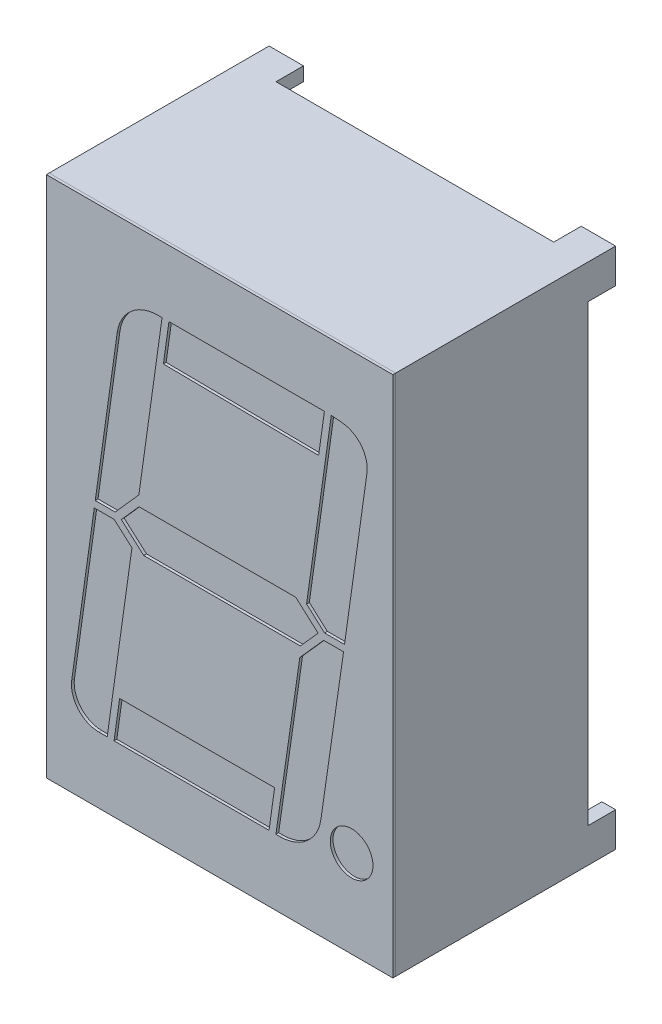
SolidWorks part; units mm, degrees
ref_plane "Front Plane" through (0, 0, 0) normal (0, 0, 1) x (1, 0, 0)
ref_plane "Top Plane" through (0, 0, 0) normal (0, 1, 0) x (1, 0, 0)
ref_plane "Right Plane" through (0, 0, 0) normal (1, 0, 0) x (0, 0, -1)
sketch "Sketch1" plane through (0, 0, 0) normal (0, 0, 1) x (1, 0, 0)
  line L1 (-6.3, -9.5) -> (6.3, -9.5)
  line L2 (-6.3, -9.5) -> (-6.3, 9.5)
  line L3 (-6.3, 9.5) -> (6.3, 9.5)
  line L4 (6.3, -9.5) -> (6.3, 9.5)
  line L5 (-6.3, -9.5) -> (6.3, 9.5) construction
  line L6 (-6.3, 9.5) -> (6.3, -9.5) construction
  point P0 (0, 0)
  dimension "D1" = 12.6
  dimension "D2" = 19
extrude "Boss-Extrude1" add sketch "Sketch1" along normal blind 7
sketch "Sketch2" plane through (0, 0, 0) normal (0, 0, -1) x (-1, 0, 0)
  line L0 (-6.3, 9.5) -> (-5.05, 9.5)
  line L1 (-6.3, 9.5) -> (6.3, 9.5) construction
  line L2 (-5.05, 9.5) -> (-5.05, 9)
  line L3 (-5.05, 9) -> (-5.8, 9)
  line L4 (-5.8, 9) -> (-5.8, 8.25)
  line L5 (-5.8, 8.25) -> (-6.3, 8.25)
  line L6 (-6.3, -9.5) -> (-6.3, 9.5) construction
  line L7 (-6.3, 8.25) -> (-6.3, 9.5)
  line L8 (0, 0) -> (0, 16.9715) construction
  line L9 (5.05, 9.5) -> (5.05, 9)
  line L10 (5.05, 9) -> (5.8, 9)
  line L11 (5.8, 9) -> (5.8, 8.25)
  line L12 (5.8, 8.25) -> (6.3, 8.25)
  line L13 (6.3, 8.25) -> (6.3, 9.5)
  line L14 (6.3, 9.5) -> (5.05, 9.5)
  line L15 (-6.942, 0) -> (9.2784, 0) construction
  line L16 (6.3, -8.25) -> (6.3, -9.5)
  line L17 (5.8, -8.25) -> (6.3, -8.25)
  line L18 (5.8, -9) -> (5.8, -8.25)
  line L19 (5.05, -9) -> (5.8, -9)
  line L20 (5.05, -9.5) -> (5.05, -9)
  line L21 (6.3, -9.5) -> (5.05, -9.5)
  line L22 (-5.05, -9.5) -> (-5.05, -9)
  line L23 (-5.8, -8.25) -> (-6.3, -8.25)
  line L24 (-5.8, -9) -> (-5.8, -8.25)
  line L25 (-5.05, -9) -> (-5.8, -9)
  line L26 (-6.3, -9.5) -> (-5.05, -9.5)
  line L27 (-6.3, -8.25) -> (-6.3, -9.5)
  dimension "D1" = 0.75
  dimension "D2" = 0.5
extrude "Boss-Extrude2" add sketch "Sketch2" along normal blind 1
sketch "Sketch3" plane through (0, 0, 7) normal (0, 0, 1) x (1, 0, 0)
  line L1 (-6.3, -9.5) -> (6.3, -9.5)
  line L2 (-6.3, -9.5) -> (-6.3, 9.5)
  line L3 (-6.3, 9.5) -> (6.3, 9.5)
  line L4 (6.3, -9.5) -> (6.3, 9.5)
  line L5 (-6.3, -9.5) -> (6.3, 9.5) construction
  line L6 (-6.3, 9.5) -> (6.3, -9.5) construction
  point P0 (0, 0)
extrude "Boss-Extrude3" add sketch "Sketch3" along normal blind 0.1 separate body
sketch "Sketch4" plane through (0, 0, 7.1) normal (0, 0, 1) x (1, 0, 0)
  line L0 (6.3, -9.5) -> (6.3, 9.5) construction
  line L1 (-4.8, -7.1) -> (4.8, -7.1) construction
  line L2 (-4.8, -7.1) -> (-4.8, 7.1) construction
  line L3 (-4.8, 7.1) -> (4.8, 7.1) construction
  line L4 (4.8, -7.1) -> (4.8, 7.1) construction
  line L5 (-4.8, -7.1) -> (4.8, 7.1) construction
  line L6 (-4.8, 7.1) -> (4.8, -7.1) construction
  line L7 (-5.8855, -9.5697) -> (-3.2686, 9.0505) construction
  line L8 (5.8697, 9.573) -> (3.0174, -10.7223) construction
  line L9 (-1.8427, 7.1) -> (3.81, 7.1)
  line L10 (-1.8427, 7.1) -> (-2.0445, 5.6641)
  line L11 (3.81, 7.1) -> (3.6002, 5.6069)
  line L12 (-2.0445, 5.6641) -> (3.6002, 5.6069)
  line L13 (7.6574, 0) -> (-12.0266, 0) construction
  line L14 (-3.7242, 5.8088) -> (-4.523, 0.125)
  line L15 (-5.3783, -5.9608) -> (-4.5581, -0.125)
  line L16 (-4.388, -7.1) -> (-4.0884, -7.1)
  line L17 (-2.0927, 7.1) -> (-2.2388, 7.1)
  line L18 (4.4537, 7.0659) -> (4.06, 7.1)
  line L19 (5.3578, 5.9305) -> (4.5419, 0.125)
  line L20 (2.0468, -7.1) -> (2.1984, -7.1)
  line L21 (3.6829, -5.8149) -> (4.5068, -0.125)
  line L22 (-4.523, 0.125) -> (-3.798, 0.125)
  line L23 (-4.5581, -0.125) -> (-3.8331, -0.125)
  line L24 (-2.93, 0.725) -> (2.7658, 0.725)
  line L25 (-2.7591, -0.725) -> (2.9366, -0.725)
  line L26 (-2.0927, 7.1) -> (-2.9368, 1.0936)
  line L27 (-2.9368, 1.0936) -> (-3.798, 0.125)
  line L28 (-2.93, 0.725) -> (-3.5746, 0)
  line L29 (-3.5746, 0) -> (-2.7591, -0.725)
  line L30 (-4.0884, -7.1) -> (-3.1886, -0.698)
  line L31 (0, 12.4056) -> (0, -14.261) construction
  line L32 (-3.8331, -0.125) -> (-3.1886, -0.698)
  line L33 (2.7658, 0.725) -> (3.5812, 0)
  line L34 (3.5812, 0) -> (2.9366, -0.725)
  line L35 (4.5419, 0.125) -> (3.8169, 0.125)
  line L36 (4.06, 7.1) -> (3.1616, 0.7076)
  line L37 (3.1616, 0.7076) -> (3.8169, 0.125)
  line L38 (4.5068, -0.125) -> (3.7818, -0.125)
  line L39 (2.0468, -7.1) -> (2.9157, -1.0991)
  line L40 (3.7818, -0.125) -> (2.9157, -1.0991)
  line L41 (-3.8384, -7.1) -> (1.7968, -7.1)
  line L42 (-3.8384, -7.1) -> (-3.6366, -5.6641)
  line L43 (1.7968, -7.1) -> (1.9996, -5.6569)
  line L44 (-3.6366, -5.6641) -> (1.9996, -5.6569)
  arc A0 (-2.2388, 7.1) -> (-3.7242, 5.8088) centre (-2.2388, 5.6) ccw
  arc A1 (3.6829, -5.8149) -> (2.1984, -7.1) centre (2.1984, -5.6) cw
  arc A2 (-5.3783, -5.9608) -> (-4.388, -7.1) centre (-4.388, -6.1) ccw
  arc A3 (5.3578, 5.9305) -> (4.4537, 7.0659) centre (4.3675, 6.0697) ccw
  circle A4 centre (4.8, -6.324) radius 0.776
  point P0 (0, 0)
  point P53 (-3.5427, 7.1)
  point P56 (3.4968, -7.1)
  point P59 (-5.5384, -7.1)
  point P62 (5.5046, 6.975)
  dimension "D25" = 1.5
  dimension "D26" = 1.5
  dimension "D27" = 1
  dimension "D1" = 14.2
  dimension "D2" = 1.5
  dimension "D3" = 8
  dimension "D4" = 1.45
  dimension "D5" = 0.25
  dimension "D6" = 1.45
  dimension "D7" = 0.25
  dimension "D8" = 1.45
  dimension "D9" = 1.45
  dimension "D10" = 1.45
  dimension "D11" = 0.725
  dimension "D12" = 1.45
  dimension "D13" = 0.125
  dimension "D14" = 0.125
  dimension "D15" = 0.725
  dimension "D16" = 0.25
  dimension "D17" = 0.725
  dimension "D18" = 0.25
  dimension "D19" = 0.125
  dimension "D20" = 0.725
  dimension "D21" = 0.725
  dimension "D22" = 0.25
  dimension "D23" = 0.25
  dimension "D24" = 1.45
  dimension "D28" = 0.125
extrude "Cut-Extrude1" cut sketch "Sketch4" against normal up to next (0.1 mm away)
